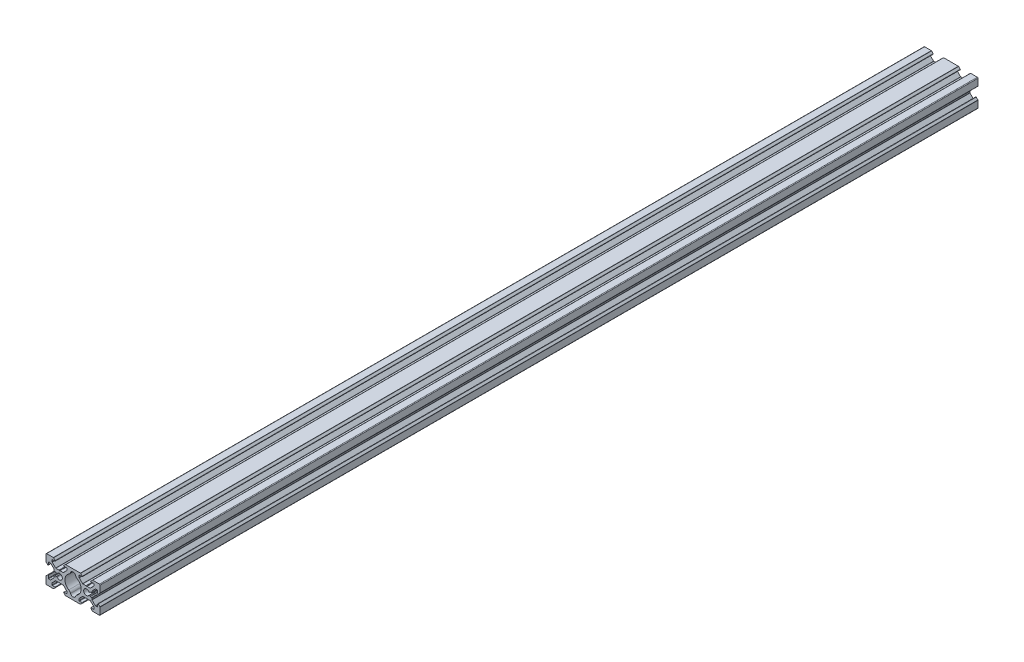
SolidWorks part; units mm, degrees
ref_plane "Front Plane" through (0, 0, 0) normal (0, 0, 1) x (1, 0, 0)
ref_plane "Top Plane" through (0, 0, 0) normal (0, 1, 0) x (1, 0, 0)
ref_plane "Right Plane" through (0, 0, 0) normal (1, 0, 0) x (0, 0, -1)
sketch "Model" plane through (0, 0, 0) normal (0, 0, 1) x (1, 0, 0)
  line L188 (2260.9191, 1499.2537) -> (2259.5984, 1499.2537)
  line L189 (2259.3484, 1499.0037) -> (2259.3484, 1497.1537)
  line L190 (2258.9216, 1496.9769) -> (2257.7363, 1498.1623)
  line L191 (2257.6484, 1498.3744) -> (2257.6484, 1503.3037)
  line L192 (2258.1484, 1503.8037) -> (2263.0777, 1503.8037)
  line L193 (2263.2898, 1503.7158) -> (2264.4752, 1502.5305)
  line L194 (2264.2984, 1502.1037) -> (2262.4484, 1502.1037)
  line L195 (2262.1984, 1501.8537) -> (2262.1984, 1500.533)
  line L196 (2262.2716, 1500.3562) -> (2264.751, 1497.8769)
  line L197 (2264.9278, 1497.8037) -> (2267.1874, 1497.8037)
  line L198 (2268.1094, 1497.8037) -> (2270.3691, 1497.8037)
  line L199 (2270.5459, 1497.8769) -> (2273.0252, 1500.3562)
  line L200 (2273.0984, 1500.533) -> (2273.0984, 1501.8537)
  line L201 (2272.8484, 1502.1037) -> (2270.9984, 1502.1037)
  line L202 (2270.8216, 1502.5305) -> (2272.007, 1503.7158)
  line L203 (2272.2191, 1503.8037) -> (2283.0777, 1503.8037)
  line L204 (2283.2898, 1503.7158) -> (2284.4752, 1502.5305)
  line L205 (2284.2984, 1502.1037) -> (2282.4484, 1502.1037)
  line L206 (2282.1984, 1501.8537) -> (2282.1984, 1500.533)
  line L207 (2282.2716, 1500.3562) -> (2284.751, 1497.8769)
  line L208 (2284.9278, 1497.8037) -> (2287.1874, 1497.8037)
  line L209 (2288.1094, 1497.8037) -> (2290.3691, 1497.8037)
  line L210 (2290.5459, 1497.8769) -> (2293.0252, 1500.3562)
  line L211 (2293.0984, 1500.533) -> (2293.0984, 1501.8537)
  line L212 (2292.8484, 1502.1037) -> (2290.9984, 1502.1037)
  line L213 (2290.8216, 1502.5305) -> (2292.007, 1503.7158)
  line L214 (2292.2191, 1503.8037) -> (2297.1484, 1503.8037)
  line L215 (2297.6484, 1503.3037) -> (2297.6484, 1498.3744)
  line L216 (2297.5606, 1498.1623) -> (2296.3752, 1496.9769)
  line L217 (2295.9484, 1497.1537) -> (2295.9484, 1499.0037)
  line L218 (2295.6984, 1499.2537) -> (2294.3778, 1499.2537)
  line L219 (2294.201, 1499.1805) -> (2291.7363, 1496.7158)
  line L220 (2291.6484, 1496.5037) -> (2291.6484, 1495.6037)
  line L221 (2291.3484, 1495.3037) -> (2290.4485, 1495.3037)
  line L222 (2290.2363, 1495.2158) -> (2289.8912, 1494.8707)
  line L223 (2289.8912, 1492.7366) -> (2290.2363, 1492.3916)
  line L224 (2290.4485, 1492.3037) -> (2291.3484, 1492.3037)
  line L225 (2291.6484, 1492.0037) -> (2291.6484, 1491.1037)
  line L226 (2291.7363, 1490.8916) -> (2294.201, 1488.4269)
  line L227 (2294.3778, 1488.3537) -> (2295.6984, 1488.3537)
  line L228 (2295.9484, 1488.6037) -> (2295.9484, 1490.4537)
  line L229 (2296.3752, 1490.6305) -> (2297.5606, 1489.4451)
  line L230 (2297.6484, 1489.233) -> (2297.6484, 1484.3037)
  line L231 (2297.1484, 1483.8037) -> (2292.2191, 1483.8037)
  line L232 (2292.007, 1483.8916) -> (2290.8216, 1485.0769)
  line L233 (2290.9984, 1485.5037) -> (2292.8484, 1485.5037)
  line L234 (2293.0984, 1485.7537) -> (2293.0984, 1487.0744)
  line L235 (2293.0252, 1487.2511) -> (2290.5459, 1489.7305)
  line L236 (2290.3691, 1489.8037) -> (2288.1094, 1489.8037)
  line L237 (2287.1874, 1489.8037) -> (2284.9278, 1489.8037)
  line L238 (2284.751, 1489.7305) -> (2282.2716, 1487.2511)
  line L239 (2282.1984, 1487.0744) -> (2282.1984, 1485.7537)
  line L240 (2282.4484, 1485.5037) -> (2284.2984, 1485.5037)
  line L241 (2284.4752, 1485.0769) -> (2283.2898, 1483.8916)
  line L242 (2283.0777, 1483.8037) -> (2272.2191, 1483.8037)
  line L243 (2272.007, 1483.8916) -> (2270.8216, 1485.0769)
  line L244 (2270.9984, 1485.5037) -> (2272.8484, 1485.5037)
  line L245 (2273.0984, 1485.7537) -> (2273.0984, 1487.0744)
  line L246 (2273.0252, 1487.2511) -> (2270.5459, 1489.7305)
  line L247 (2270.3691, 1489.8037) -> (2268.1094, 1489.8037)
  line L248 (2267.1874, 1489.8037) -> (2264.9278, 1489.8037)
  line L249 (2264.751, 1489.7305) -> (2262.2716, 1487.2511)
  line L250 (2262.1984, 1487.0744) -> (2262.1984, 1485.7537)
  line L251 (2262.4484, 1485.5037) -> (2264.2984, 1485.5037)
  line L252 (2264.4752, 1485.0769) -> (2263.2898, 1483.8916)
  line L253 (2263.0777, 1483.8037) -> (2258.1484, 1483.8037)
  line L254 (2257.6484, 1484.3037) -> (2257.6484, 1489.233)
  line L255 (2257.7363, 1489.4451) -> (2258.9216, 1490.6305)
  line L256 (2259.3484, 1490.4537) -> (2259.3484, 1488.6037)
  line L257 (2259.5984, 1488.3537) -> (2260.9191, 1488.3537)
  line L258 (2261.0959, 1488.4269) -> (2263.5606, 1490.8916)
  line L259 (2263.6484, 1491.1037) -> (2263.6484, 1492.0037)
  line L260 (2263.9484, 1492.3037) -> (2264.8484, 1492.3037)
  line L261 (2265.0605, 1492.3916) -> (2265.4056, 1492.7366)
  line L262 (2265.4056, 1494.8707) -> (2265.0605, 1495.2158)
  line L263 (2264.8484, 1495.3037) -> (2263.9484, 1495.3037)
  line L264 (2263.6484, 1495.6037) -> (2263.6484, 1496.5037)
  line L265 (2263.5606, 1496.7158) -> (2261.0959, 1499.1805)
  arc A322 (2259.5984, 1499.2537) -> (2259.3484, 1499.0037) centre (2259.5984, 1499.0037) ccw
  arc A323 (2258.9216, 1496.9769) -> (2259.3484, 1497.1537) centre (2259.0984, 1497.1537) ccw
  arc A324 (2257.6484, 1498.3744) -> (2257.7363, 1498.1623) centre (2257.9484, 1498.3744) ccw
  arc A325 (2258.1484, 1503.8037) -> (2257.6484, 1503.3037) centre (2258.1484, 1503.3037) ccw
  arc A326 (2263.2898, 1503.7158) -> (2263.0777, 1503.8037) centre (2263.0777, 1503.5037) ccw
  arc A327 (2264.2984, 1502.1037) -> (2264.4752, 1502.5305) centre (2264.2984, 1502.3537) ccw
  arc A328 (2262.4484, 1502.1037) -> (2262.1984, 1501.8537) centre (2262.4484, 1501.8537) ccw
  arc A329 (2262.1984, 1500.533) -> (2262.2716, 1500.3562) centre (2262.4484, 1500.533) ccw
  arc A330 (2264.751, 1497.8769) -> (2264.9278, 1497.8037) centre (2264.9278, 1498.0537) ccw
  arc A331 (2267.4389, 1497.6673) -> (2267.1874, 1497.8037) centre (2267.1874, 1497.5037) ccw
  arc A332 (2267.4389, 1497.6673) -> (2267.858, 1497.6673) centre (2267.6484, 1497.8037) ccw
  arc A333 (2268.1094, 1497.8037) -> (2267.858, 1497.6673) centre (2268.1094, 1497.5037) ccw
  arc A334 (2270.3691, 1497.8037) -> (2270.5459, 1497.8769) centre (2270.3691, 1498.0537) ccw
  arc A335 (2273.0252, 1500.3562) -> (2273.0984, 1500.533) centre (2272.8484, 1500.533) ccw
  arc A336 (2273.0984, 1501.8537) -> (2272.8484, 1502.1037) centre (2272.8484, 1501.8537) ccw
  arc A337 (2270.8216, 1502.5305) -> (2270.9984, 1502.1037) centre (2270.9984, 1502.3537) ccw
  arc A338 (2272.2191, 1503.8037) -> (2272.007, 1503.7158) centre (2272.2191, 1503.5037) ccw
  arc A339 (2283.2898, 1503.7158) -> (2283.0777, 1503.8037) centre (2283.0777, 1503.5037) ccw
  arc A340 (2284.2984, 1502.1037) -> (2284.4752, 1502.5305) centre (2284.2984, 1502.3537) ccw
  arc A341 (2282.4484, 1502.1037) -> (2282.1984, 1501.8537) centre (2282.4484, 1501.8537) ccw
  arc A342 (2282.1984, 1500.533) -> (2282.2716, 1500.3562) centre (2282.4484, 1500.533) ccw
  arc A343 (2284.751, 1497.8769) -> (2284.9278, 1497.8037) centre (2284.9278, 1498.0537) ccw
  arc A344 (2287.4389, 1497.6673) -> (2287.1874, 1497.8037) centre (2287.1874, 1497.5037) ccw
  arc A345 (2287.4389, 1497.6673) -> (2287.858, 1497.6673) centre (2287.6484, 1497.8037) ccw
  arc A346 (2288.1094, 1497.8037) -> (2287.858, 1497.6673) centre (2288.1094, 1497.5037) ccw
  arc A347 (2290.3691, 1497.8037) -> (2290.5459, 1497.8769) centre (2290.3691, 1498.0537) ccw
  arc A348 (2293.0252, 1500.3562) -> (2293.0984, 1500.533) centre (2292.8484, 1500.533) ccw
  arc A349 (2293.0984, 1501.8537) -> (2292.8484, 1502.1037) centre (2292.8484, 1501.8537) ccw
  arc A350 (2290.8216, 1502.5305) -> (2290.9984, 1502.1037) centre (2290.9984, 1502.3537) ccw
  arc A351 (2292.2191, 1503.8037) -> (2292.007, 1503.7158) centre (2292.2191, 1503.5037) ccw
  arc A352 (2297.6484, 1503.3037) -> (2297.1484, 1503.8037) centre (2297.1484, 1503.3037) ccw
  arc A353 (2297.5606, 1498.1623) -> (2297.6484, 1498.3744) centre (2297.3484, 1498.3744) ccw
  arc A354 (2295.9484, 1497.1537) -> (2296.3752, 1496.9769) centre (2296.1984, 1497.1537) ccw
  arc A355 (2295.9484, 1499.0037) -> (2295.6984, 1499.2537) centre (2295.6984, 1499.0037) ccw
  arc A356 (2294.3778, 1499.2537) -> (2294.201, 1499.1805) centre (2294.3778, 1499.0037) ccw
  arc A357 (2291.7363, 1496.7158) -> (2291.6484, 1496.5037) centre (2291.9484, 1496.5037) ccw
  arc A358 (2291.3484, 1495.3037) -> (2291.6484, 1495.6037) centre (2291.3484, 1495.6037) ccw
  arc A359 (2290.4485, 1495.3037) -> (2290.2363, 1495.2158) centre (2290.4485, 1495.0037) ccw
  arc A360 (2289.4253, 1494.923) -> (2289.8912, 1494.8707) centre (2289.6791, 1495.0829) ccw
  arc A361 (2289.4253, 1494.923) -> (2289.4253, 1492.6844) centre (2287.6484, 1493.8037) ccw
  arc A362 (2289.8912, 1492.7366) -> (2289.4253, 1492.6844) centre (2289.6791, 1492.5245) ccw
  arc A363 (2290.2363, 1492.3916) -> (2290.4485, 1492.3037) centre (2290.4485, 1492.6037) ccw
  arc A364 (2291.6484, 1492.0037) -> (2291.3484, 1492.3037) centre (2291.3484, 1492.0037) ccw
  arc A365 (2291.6484, 1491.1037) -> (2291.7363, 1490.8916) centre (2291.9484, 1491.1037) ccw
  arc A366 (2294.201, 1488.4269) -> (2294.3778, 1488.3537) centre (2294.3778, 1488.6037) ccw
  arc A367 (2295.6984, 1488.3537) -> (2295.9484, 1488.6037) centre (2295.6984, 1488.6037) ccw
  arc A368 (2296.3752, 1490.6305) -> (2295.9484, 1490.4537) centre (2296.1984, 1490.4537) ccw
  arc A369 (2297.6484, 1489.233) -> (2297.5606, 1489.4451) centre (2297.3484, 1489.233) ccw
  arc A370 (2297.1484, 1483.8037) -> (2297.6484, 1484.3037) centre (2297.1484, 1484.3037) ccw
  arc A371 (2292.007, 1483.8916) -> (2292.2191, 1483.8037) centre (2292.2191, 1484.1037) ccw
  arc A372 (2290.9984, 1485.5037) -> (2290.8216, 1485.0769) centre (2290.9984, 1485.2537) ccw
  arc A373 (2292.8484, 1485.5037) -> (2293.0984, 1485.7537) centre (2292.8484, 1485.7537) ccw
  arc A374 (2293.0984, 1487.0744) -> (2293.0252, 1487.2511) centre (2292.8484, 1487.0744) ccw
  arc A375 (2290.5459, 1489.7305) -> (2290.3691, 1489.8037) centre (2290.3691, 1489.5537) ccw
  arc A376 (2287.858, 1489.9401) -> (2288.1094, 1489.8037) centre (2288.1094, 1490.1037) ccw
  arc A377 (2287.858, 1489.9401) -> (2287.4389, 1489.9401) centre (2287.6484, 1489.8037) ccw
  arc A378 (2287.1874, 1489.8037) -> (2287.4389, 1489.9401) centre (2287.1874, 1490.1037) ccw
  arc A379 (2284.9278, 1489.8037) -> (2284.751, 1489.7305) centre (2284.9278, 1489.5537) ccw
  arc A380 (2282.2716, 1487.2511) -> (2282.1984, 1487.0744) centre (2282.4484, 1487.0744) ccw
  arc A381 (2282.1984, 1485.7537) -> (2282.4484, 1485.5037) centre (2282.4484, 1485.7537) ccw
  arc A382 (2284.4752, 1485.0769) -> (2284.2984, 1485.5037) centre (2284.2984, 1485.2537) ccw
  arc A383 (2283.0777, 1483.8037) -> (2283.2898, 1483.8916) centre (2283.0777, 1484.1037) ccw
  arc A384 (2272.007, 1483.8916) -> (2272.2191, 1483.8037) centre (2272.2191, 1484.1037) ccw
  arc A385 (2270.9984, 1485.5037) -> (2270.8216, 1485.0769) centre (2270.9984, 1485.2537) ccw
  arc A386 (2272.8484, 1485.5037) -> (2273.0984, 1485.7537) centre (2272.8484, 1485.7537) ccw
  arc A387 (2273.0984, 1487.0744) -> (2273.0252, 1487.2511) centre (2272.8484, 1487.0744) ccw
  arc A388 (2270.5459, 1489.7305) -> (2270.3691, 1489.8037) centre (2270.3691, 1489.5537) ccw
  arc A389 (2267.858, 1489.9401) -> (2268.1094, 1489.8037) centre (2268.1094, 1490.1037) ccw
  arc A390 (2267.858, 1489.9401) -> (2267.4389, 1489.9401) centre (2267.6484, 1489.8037) ccw
  arc A391 (2267.1874, 1489.8037) -> (2267.4389, 1489.9401) centre (2267.1874, 1490.1037) ccw
  arc A392 (2264.9278, 1489.8037) -> (2264.751, 1489.7305) centre (2264.9278, 1489.5537) ccw
  arc A393 (2262.2716, 1487.2511) -> (2262.1984, 1487.0744) centre (2262.4484, 1487.0744) ccw
  arc A394 (2262.1984, 1485.7537) -> (2262.4484, 1485.5037) centre (2262.4484, 1485.7537) ccw
  arc A395 (2264.4752, 1485.0769) -> (2264.2984, 1485.5037) centre (2264.2984, 1485.2537) ccw
  arc A396 (2263.0777, 1483.8037) -> (2263.2898, 1483.8916) centre (2263.0777, 1484.1037) ccw
  arc A397 (2257.6484, 1484.3037) -> (2258.1484, 1483.8037) centre (2258.1484, 1484.3037) ccw
  arc A398 (2257.7363, 1489.4451) -> (2257.6484, 1489.233) centre (2257.9484, 1489.233) ccw
  arc A399 (2259.3484, 1490.4537) -> (2258.9216, 1490.6305) centre (2259.0984, 1490.4537) ccw
  arc A400 (2259.3484, 1488.6037) -> (2259.5984, 1488.3537) centre (2259.5984, 1488.6037) ccw
  arc A401 (2260.9191, 1488.3537) -> (2261.0959, 1488.4269) centre (2260.9191, 1488.6037) ccw
  arc A402 (2263.5606, 1490.8916) -> (2263.6484, 1491.1037) centre (2263.3484, 1491.1037) ccw
  arc A403 (2263.9484, 1492.3037) -> (2263.6484, 1492.0037) centre (2263.9484, 1492.0037) ccw
  arc A404 (2264.8484, 1492.3037) -> (2265.0605, 1492.3916) centre (2264.8484, 1492.6037) ccw
  arc A405 (2265.8716, 1492.6844) -> (2265.4056, 1492.7366) centre (2265.6177, 1492.5245) ccw
  arc A406 (2265.8716, 1492.6844) -> (2265.8716, 1494.923) centre (2267.6484, 1493.8037) ccw
  arc A407 (2265.4056, 1494.8707) -> (2265.8716, 1494.923) centre (2265.6177, 1495.0829) ccw
  arc A408 (2265.0605, 1495.2158) -> (2264.8484, 1495.3037) centre (2264.8484, 1495.0037) ccw
  arc A409 (2263.6484, 1495.6037) -> (2263.9484, 1495.3037) centre (2263.9484, 1495.6037) ccw
  arc A410 (2263.6484, 1496.5037) -> (2263.5606, 1496.7158) centre (2263.3484, 1496.5037) ccw
  arc A411 (2261.0959, 1499.1805) -> (2260.9191, 1499.2537) centre (2260.9191, 1499.0037) ccw
  arc A412 (2275.7743, 1487.1053) -> (2274.4574, 1488.7226) centre (2272.7289, 1485.9704) ccw
  arc A413 (2275.7743, 1487.1053) -> (2279.5225, 1487.1053) centre (2277.6484, 1487.8037) ccw
  arc A414 (2280.8394, 1488.7226) -> (2279.5225, 1487.1053) centre (2282.5679, 1485.9704) ccw
  arc A415 (2280.8394, 1488.7226) -> (2280.8394, 1498.8848) centre (2277.6484, 1493.8037) ccw
  arc A416 (2279.5225, 1500.5021) -> (2280.8394, 1498.8848) centre (2282.5679, 1501.637) ccw
  arc A417 (2279.5225, 1500.5021) -> (2275.7743, 1500.5021) centre (2277.6484, 1499.8037) ccw
  arc A418 (2274.4574, 1498.8848) -> (2275.7743, 1500.5021) centre (2272.7289, 1501.637) ccw
  arc A419 (2274.4574, 1498.8848) -> (2274.4574, 1488.7226) centre (2277.6484, 1493.8037) ccw
extrude "Boss-Extrude1" add sketch "Model" along normal blind 650
equation "\"x_length\"=1000"
